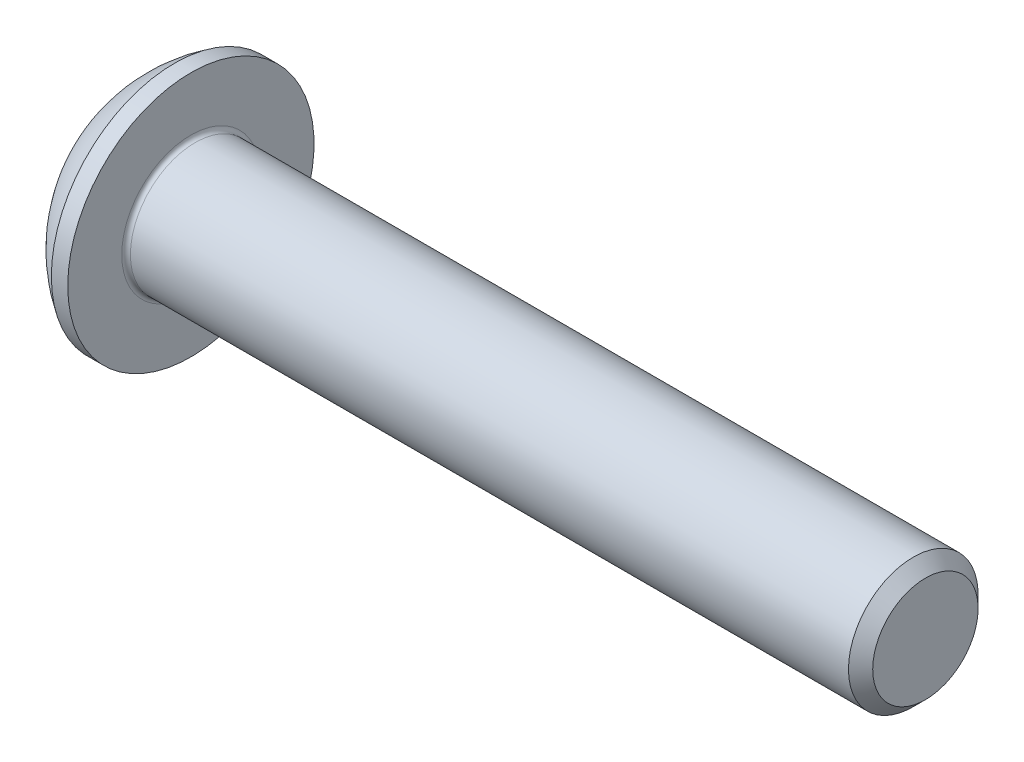
SolidWorks part; units mm, degrees
ref_plane "Plane1" through (0, 0, 0) normal (0, 0, 1) x (1, 0, 0)
ref_plane "Plane2" through (0, 0, 0) normal (0, 1, 0) x (1, 0, 0)
ref_plane "Plane3" through (0, 0, 0) normal (1, 0, 0) x (0, 0, -1)
revolve "BaseBody" add sketch "BodySke" angle 360 about L4
sketch "BodySke" plane through (0, 0, 0) normal (0, 0, 1) x (1, 0, 0)
  line L0 (18.65, 0) -> (18.65, 1.2195)
  line L1 (18.3695, 1.5) -> (1.65, 1.5)
  line L2 (1.65, 1.5) -> (1.65, 2.85)
  line L3 (1.65, 2.85) -> (1.27, 2.85)
  line L4 (0, 0) -> (101.6, 0) construction
  line L5 (1.65, -2.85) -> (1.27, -2.85) construction
  line L6 (55.6768, -1.5) -> (1.65, -1.5) construction
  line L7 (18.65, 0) -> (0, 0)
  line L8 (0, 1.425) -> (0, -1.425) construction
  line L9 (0, 0) -> (0, 1.425)
  line L10 (18.65, 1.2195) -> (18.3695, 1.5)
  line L11 (18.65, -1.2195) -> (18.3695, -1.5) construction
  line L12 (2.15, 9.525) -> (2.15, -1.5) construction
  line L13 (10.65, 9.525) -> (10.65, -1.5) construction
  arc A1 (0, 1.425) -> (1.27, 2.85) centre (3.0334, 0) cw
  dimension "D1" = 2.85
  dimension "Diameter" = 3
  dimension "Length" = 17
  dimension "Head_dia" = 5.7
  dimension "Head_ht" = 1.65
  dimension "Head_side_ht" = 0.38
  dimension "Minor_dia" = 2.439
  dimension "Body_ch_ang" = 45
  dimension "Advance" = 0.5
  dimension "Thread_nom" = 8
cosmetic thread "ThreadCosmetic" [suppressed] parameters "Thread_length"=8, "Thread_minor"=2.439
fillet "Fillet1" radius 0.1 1 edges at (1.65, 0, 1.5)
sketch "Sketch2" plane through (0, 0, 0) normal (0, 0, 1) x (1, 0, 0)
  line L0 (0, 1) -> (1.04, 1)
  line L1 (1.04, 1) -> (1.6174, 0)
  line L3 (1.6174, 0) -> (0, 0)
  line L4 (0, 0) -> (0, 1)
  line L5 (0, -1) -> (1.04, -1) construction
  line L6 (0, 0) -> (47.625, 0) construction
  dimension "D2" = 60
  dimension "PreBroach_depth" = 1.04
  dimension "PreBroach_dia" = 2
revolve "PreBroach" cut sketch "Sketch2" angle 360 about L6
sketch "Sketch3" plane through (0, 0, 0) normal (1, 0, 0) x (0, 0, -1)
  line L0 (-1, -0.5774) -> (-1, 0.5774)
  line L1 (-1, 0.5774) -> (0, 1.1547)
  line L2 (0, 1.1547) -> (1, 0.5774)
  line L3 (1, 0.5774) -> (1, -0.5774)
  line L4 (1, -0.5774) -> (0, -1.1547)
  line L5 (0, -1.1547) -> (-1, -0.5774)
  dimension "D1" = 1
  dimension "D2" = 1
  dimension "D3" = 2
  dimension "Hex_size" = 2
extrude "Hex" cut sketch "Sketch3" along normal blind 1.04
sketch "ThdSchSke" plane through (0, 0, 0) normal (0, 0, 1) x (1, 0, 0)
  line L0 (10.65, -1.2195) -> (10.4536, -1.5)
  line L1 (10.65, -1.2195) -> (10.8464, -1.5)
  line L2 (10.8464, -1.5) -> (10.8464, -1.875)
  line L3 (-3.175, 0) -> (5.1513, 0) construction
  line L5 (10.8464, -1.875) -> (10.4536, -1.875)
  line L6 (10.4536, -1.875) -> (10.4536, -1.5)
  dimension "Thread_minor" = 2.439
  dimension "Diameter" = 3
  dimension "Start" = 10.65
  dimension "SideAngle" = 55
  dimension "VeeAngle" = 70
  dimension "Overcut" = 3.75
revolve "ThreadSchematic" [suppressed] cut sketch "ThdSchSke" angle 360 about L3
pattern_linear "ThdSchPat" [suppressed]
equation "\"D1@BodySke\" = \"Head_dia@BodySke\" * .5"
equation "\"Thread_minor@ThreadCosmetic\" = \"Minor_dia@BodySke\""
equation "\"D1@Sketch3\" = \"Hex_size@Sketch3\" / 2"
equation "\"D2@Sketch3\" = \"D1@Sketch3\""
equation "\"D3@Sketch3\" = \"Hex_size@Sketch3\""
equation "\"Thread_length@ThreadCosmetic\" = ((sgn( (\"Length@BodySke\" - \"Advance@BodySke\" * 2.0) - \"Thread_nom@BodySke\" )-1)*( (\"Length@BodySke\" - \"Advance@BodySke\" * 2.0) - \"Thread_nom@BodySke\" ))/-2+ \"Thread_nom@BodySke\""
equation "\"Thread_minor@ThdSchSke\" = \"Minor_dia@BodySke\""
equation "\"Diameter@ThdSchSke\" = \"Diameter@BodySke\""
equation "\"Overcut@ThdSchSke\" = \"Diameter@BodySke\" * 1.25"
equation "\"Start@ThdSchSke\" = \"Head_ht@BodySke\" + \"Length@BodySke\" - \"Thread_length@ThreadCosmetic\"  '---Non-countersunk---"
equation "\"Num_threads@ThdSchPat\" = int( \"Thread_length@ThreadCosmetic\" / \"Advance@BodySke\" + 0.999 )  + 1"
equation "\"Advance@ThdSchPat\" = \"Thread_length@ThreadCosmetic\" /  (\"Num_threads@ThdSchPat\" - 1) 'relax it"
equation "\"Num_threads@ThdSchPat\" = \"Num_threads@ThdSchPat\" - sgn( \"Num_threads@ThdSchPat\" - 1) '---chamfered tips only---"
